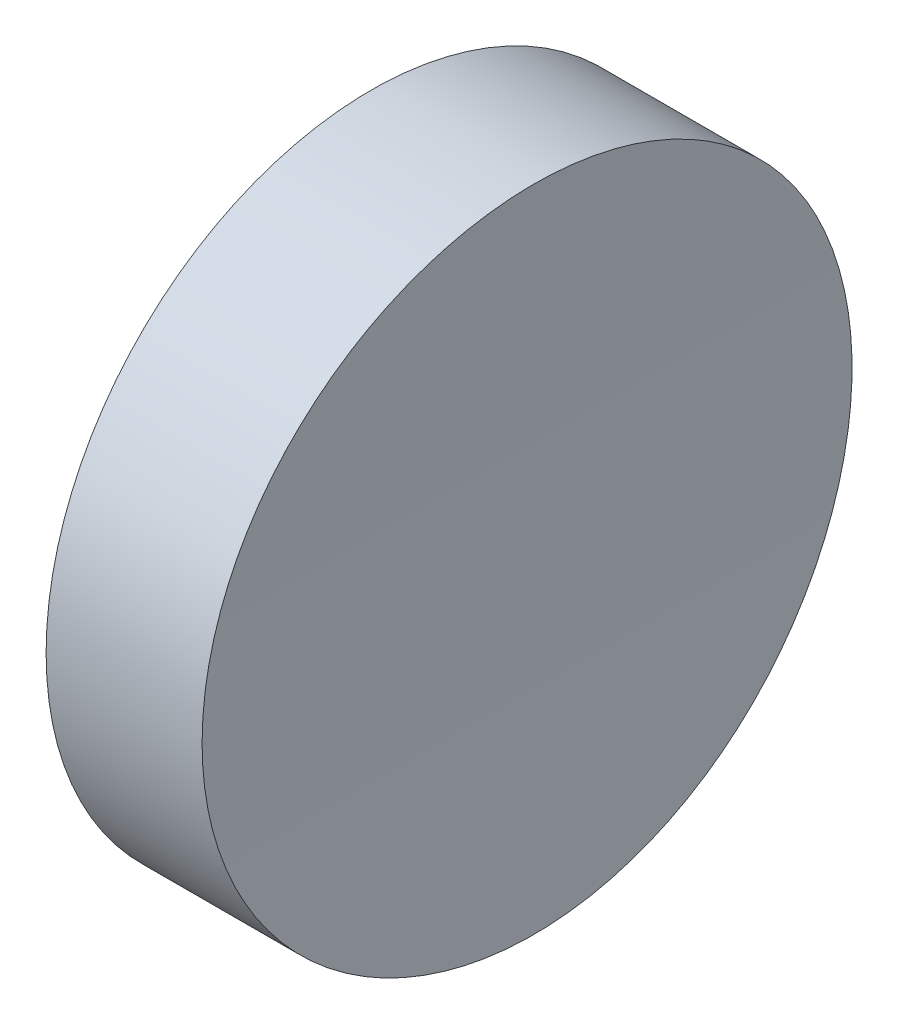
SolidWorks part; units mm, degrees
ref_plane "前视基准面" through (0, 0, 0) normal (0, 0, 1) x (1, 0, 0)
ref_plane "上视基准面" through (0, 0, 0) normal (0, 1, 0) x (1, 0, 0)
ref_plane "右视基准面" through (0, 0, 0) normal (1, 0, 0) x (0, 0, -1)
sketch "草图1" plane through (0, 0, 0) normal (1, 0, 0) x (0, 0, -1)
  circle A0 centre (0, 0) radius 12.5
  dimension "D1" = 25
extrude "凸台-拉伸1" add sketch "草图1" along normal blind 10
sketch "草图2" plane through (0, 0, 0) normal (0, 0, 1) x (1, 0, 0)
  line L0 (0, 0) -> (306, 0) construction
  line L1 (0, 0) -> (6, 0) construction
  circle A0 centre (306, 0) radius 300
  dimension "D1" = 600
  dimension "D2" = 6
extrude "切除-拉伸1" cut sketch "草图2" against normal through all both and the other way through all
